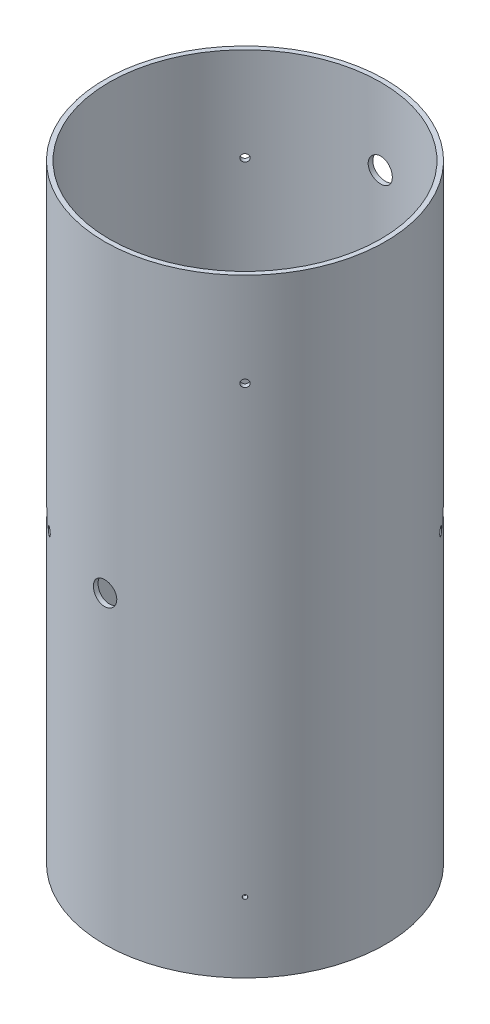
SolidWorks part; units mm, degrees
material "A-Glass Fiber"
ref_plane "Front Plane" through (0, 0, 0) normal (0, 0, 1) x (1, 0, 0)
ref_plane "Top Plane" through (0, 0, 0) normal (0, 1, 0) x (1, 0, 0)
ref_plane "Right Plane" through (0, 0, 0) normal (1, 0, 0) x (0, 0, -1)
sketch "Sketch1" plane through (0, 0, 0) normal (0, 1, 0) x (1, 0, 0)
  circle A0 centre (0, 0) radius 76.1746
  circle A1 centre (0, 0) radius 73.66
  dimension "D1" = 152.3492
  dimension "D2" = 147.32
extrude "Boss-Extrude1" add sketch "Sketch1" along normal blind 330.2
sketch "Sketch4" plane through (0, 0, 0) normal (0, 0, 1) x (1, 0, 0)
  line L0 (-76.1746, 0) -> (76.1746, 0) construction
  line L1 (76.1746, 330.2) -> (-76.1746, 330.2) construction
  line L2 (0, 330.2) -> (0, 0) construction
  line L3 (73.66, 330.2) -> (-73.66, 330.2) construction
  point P0 (0, 41.275)
  point P3 (0, 288.925)
  dimension "D1" = 41.275
  dimension "D2" = 41.275
hole_wizard "1/2 Clearance Hole5" positions "Sketch16" profile "Sketch17" hole size "1/2" standard "ANSI Inch"
sketch "Sketch16" plane through (0, 0, 0) normal (0, 0, 1) x (1, 0, 0)
  point P0 (0, 288.925)
sketch "Sketch17" plane through (0, 288.925, 0) normal (1, 0, 0) x (0, -1, 0)
  line L0 (0, 0) -> (0, 80.1345)
  line L1 (0, 80.1345) -> (6.5481, 76.2)
  line L2 (6.5481, 76.2) -> (6.5481, 0)
  line L5 (6.5481, 0) -> (0, 0)
  line L10 (0, 80.1345) -> (-6.5481, 76.2) construction
  line L11 (0, -6.35) -> (0, 107.95) construction
  dimension "Hole Dia." = 13.0962
  dimension "Hole Depth" = 76.2
  dimension "Drill Angle" = 118
sketch "Sketch27" plane through (0, 0, 0) normal (0, 0, 1) x (1, 0, 0)
  line L0 (0, 330.2) -> (0, 0) construction
  line L1 (-76.1746, 0) -> (76.1746, 0) construction
  circle A0 centre (0, 165.1) radius 6.35
  dimension "D1" = 12.7
  dimension "D2" = 165.1
extrude "Cut-Extrude1" cut sketch "Sketch27" against normal through all both and the other way through all
ref_plane "Plane1" through (0, 0, 0) normal (-0.7071, 0, 0.7071) x (0.7071, 0, 0.7071)
ref_plane "Plane2" through (0, 0, 0) normal (-0.7071, 0, 0.7071) x (0, -1, 0)
sketch "Sketch30" plane through (0, 0, 0) normal (-0.7071, 0, 0.7071) x (0.7071, 0, 0.7071)
  line L0 (0, 330.2) -> (0, 0) construction
  line L1 (4.953, 160.147) -> (-4.953, 160.147)
  line L2 (4.953, 160.147) -> (4.953, 170.053)
  line L3 (4.953, 170.053) -> (-4.953, 170.053)
  line L4 (-4.953, 160.147) -> (-4.953, 170.053)
  line L5 (4.953, 160.147) -> (-4.953, 170.053) construction
  line L6 (4.953, 170.053) -> (-4.953, 160.147) construction
  line L7 (-76.1746, 0) -> (76.1746, 0) construction
  circle A0 centre (-12.7, 165.1) radius 2.1831
  circle A1 centre (12.7, 165.1) radius 2.1831
  point P0 (0, 165.1)
  dimension "D3" = 4.3663
  dimension "D4" = 4.3663
  dimension "D1" = 9.906
  dimension "D2" = 9.906
  dimension "D5" = 12.7
  dimension "D6" = 12.7
  dimension "D7" = 165.1
extrude "Cut-Extrude2" cut sketch "Sketch30" against normal through all both and the other way through all
sketch "Sketch23" plane through (0, 0, 0) normal (-0.7071, 0, 0.7071) x (0.7071, 0, 0.7071)
  line L0 (0, 0) -> (0, 330.2) construction
  line L1 (73.66, 330.2) -> (-73.66, 330.2) construction
  line L2 (-76.1746, 165.1) -> (76.1746, 165.1) construction
  line L3 (76.1746, 0) -> (76.1746, 330.2) construction
  circle A1 centre (0, 38.1) radius 1.0922
  point P12 (0, 165.1)
  dimension "D2" = 127
extrude "Shear Scrrews" cut sketch "Sketch23" against normal through all
pattern_circular "CirPattern1" count 4 over 360 about axis through (0, 330.2, 0) along (0, -1, 0) of "Shear Scrrews"
hole_wizard "Ø4.0 (4) Diameter Hole1" positions "Sketch24" profile "Sketch25" hole size "Ø4.0" standard "ANSI Metric"
sketch "Sketch24" plane through (0, 0, 0) normal (-0.7071, 0, 0.7071) x (0, -1, 0)
  line L0 (-330.2, 76.1746) -> (-330.2, -76.1746) construction
  point P0 (-279.4, 0)
  dimension "D1" = 50.8
sketch "Sketch25" plane through (0, 279.4, 0) normal (0, 1, 0) x (-0.7071, 0, -0.7071)
  line L0 (0, 0) -> (0, 90.1017)
  line L1 (0, 90.1017) -> (2, 88.9)
  line L2 (2, 88.9) -> (2, 0)
  line L5 (2, 0) -> (0, 0)
  line L10 (0, 90.1017) -> (-2, 88.9) construction
  line L11 (0, -6.35) -> (0, 107.95) construction
  dimension "Hole Dia." = 4
  dimension "Hole Depth" = 88.9
  dimension "Drill Angle" = 118
pattern_circular "CirPattern2" count 4 over 360 about axis through (0, 330.2, 0) along (0, 1, 0) of "Ø4.0 (4) Diameter Hole1"
equation "\"Mid_Coupler_Length\" = 13in"
equation "\"D1@Boss-Extrude1\"=\"Mid_Coupler_Length\""
equation "\"Shear_Screw_Coupler_Location\" = 4.5in"
equation "\"Shear_Screw_Diameter\" = 0.086in"
equation "\"D2@Sketch23\"=\"Shear_Screw_Coupler_Location\"+0.5"
equation "\"Mid_Tube_Length\"= 1in"
equation "\"Bodytube_OD\" = 6.17in"
equation "\"Bodytube_ID\" = 5.998in"
equation "\"Camera_Cutout_Width\"=10mm"
equation "\"Camera_Cutout_Height\"=7mm"
equation "\"Fwd_Tube_Length\" = 38.5in"
equation "\"BKHD_Screw_Diam\"= 3.5mm"
equation "\"Fwd_BKHD_From_Top\" = 18in"
equation "\"Motor_OD\" = 4in"
equation "\"Aft_Section_Length\"= 36in"
equation "\"AB_Coupler_OD_Length\"= 1in"
equation "\"AB_Coupling_Section_Length\"= 0.375in"
equation "\"AB_Coupler_Length\"= \"AB_Coupler_OD_Length\" + \"AB_Coupling_Section_Length\" * 2"
equation "\"Cutout_Angle\" = 80"
equation "\"AB_Paddle_Height\" = 0.375in"
equation "\"AB_Coupler_Num_Screws\"= 4"
equation "\"AB_BKHD_Thickness\" = 0.375in"
equation "\"AB_Mount_From_Bottom\" = 23.175in"
equation "\"Num_Cutouts\" = 3"
equation "\"AB_Coupler_OD\"= 6.17in"
equation "\"AB_Coupler_ID\"= 5.75in"
equation "\"AB_Coupler_Surface_Diameter\"= 5.998in"
equation "\"AB_Coupling_Screw_Diameter\"= 0.15748in"
equation "\"AB_Central_Bushing_Length\" = .4724in"
equation "\"Lead_Screw_Dist\" = 3.4in"
equation "\"Lead_Screw_Diam\" = 0.386in"
equation "\"Lead_Screw_Length\" = (\"Mid_Coupler_Length\" + 2*0.375in + 2*.75in)"
equation "\"Paddle_Pin_Offset\" = .25in"
equation "\"Paddle_Pin_Radius\" = 2.25in"
equation "\"SS_Paddle_Pin_Radius\" = 2.25*0.66in"
equation "\"Paddle_Gear_OD\" = 3.2in"
equation "\"Drive_Gear_OD\" = 1.7in"
equation "\"Fin_Thickness\"= .118in"
equation "\"Guiderail_Cutout_Diameter\"= 1.5in"
equation "\"DB9_Hole_Dist\" = 25mm"
equation "\"DB9_Relief_Width\" = 0.47in"
equation "\"DB9_Relief_Hole_Offset\" = 0.09in"
equation "\"Airbrakes_Wire_Hole_Dia\" = .25in"
equation "\"Airbrakes_Wire_Hole_Dist\" = 1.1in"
equation "\"Servo_Gear_Offset\" = 0.5in"
equation "\"FWD_Shear_Screw_Dist\" = 1.5in"
equation "\"Camera_Screw_Dia\" = 0.216535"
equation "\"Camera_Hole_Angle\" = atn ( 2 / 3 * tan ( 12.5deg ) )"
equation "\"D2\"= \"Camera_Hole_Angle\""
equation "\"Coupler_OD\" = 5.998"
equation "\"D1@Sketch1\"=\"Coupler_OD\""
equation "\"Coupler_ID\" = 5.8"
equation "\"D2@Sketch1\"=\"Coupler_ID\""
